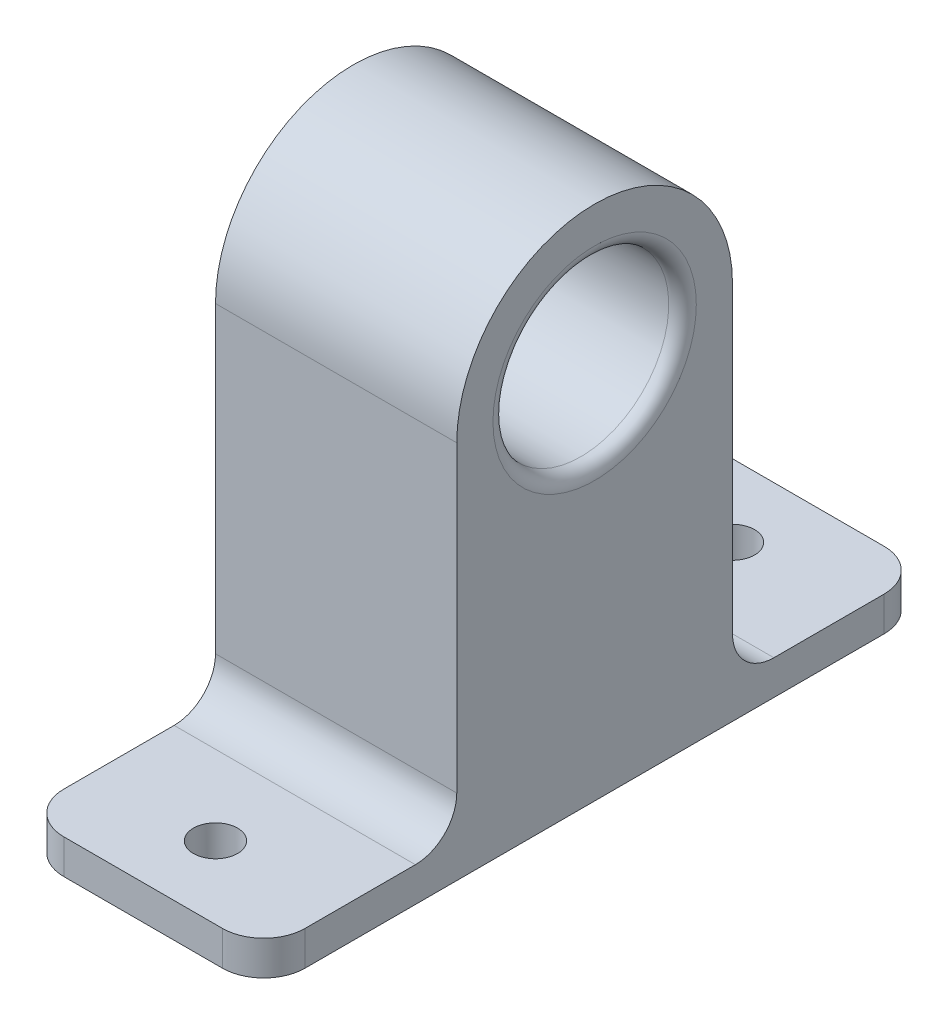
SolidWorks part; units mm, degrees
ref_plane "Front Plane" through (0, 0, 0) normal (0, 0, 1) x (1, 0, 0)
ref_plane "Top Plane" through (0, 0, 0) normal (0, 1, 0) x (1, 0, 0)
ref_plane "Right Plane" through (0, 0, 0) normal (1, 0, 0) x (0, 0, -1)
sketch "Sketch1" plane through (0, 0, 0) normal (1, 0, 0) x (0, 0, -1)
  line L0 (-48, -55) -> (-48, -50)
  line L2 (-37.5, -50) -> (-37.5, -55) construction
  line L3 (-48, -55) -> (48, -55)
  line L6 (-20, 0) -> (-20, -50)
  line L7 (-20, -50) -> (-48, -50)
  line L8 (20, -50) -> (48, -50)
  line L10 (48, -55) -> (48, -50)
  line L12 (37.5, -50) -> (37.5, -55) construction
  line L13 (0, -55) -> (0, 0) construction
  line L14 (20, -50) -> (20, 0)
  circle A0 centre (0, 0) radius 12.75 construction
  arc A1 (-20, 0) -> (20, 0) centre (0, 0) cw
  point P11 (0, -55)
  point P12 (0, 0)
  point P18 (0, 0)
  point P19 (0, 0)
  point P20 (17.7316, -9.2515)
  dimension "D1" = 25.5
  dimension "D2" = 20
  dimension "D5" = 55
  dimension "D6" = 37.5
  dimension "D3" = 28
  dimension "D4" = 5
extrude "Boss-Extrude1" add sketch "Sketch1" along normal blind 35
sketch "Sketch2" plane through (35, 0, 0) normal (1, 0, 0) x (0, 0, -1)
  circle A0 centre (0, 0) radius 12.75 construction
  circle A1 centre (0, 0) radius 12.75
extrude "Cut-Extrude1" cut sketch "Sketch2" against normal offset from surface (32 mm away) 3 up to face at (0, -36.25, 0)
sketch "Sketch3" plane through (0, 0, 0) normal (-1, 0, 0) x (0, 0, 1)
  circle A0 centre (0, 0) radius 8.5 construction
  circle A1 centre (0, 8.5) radius 1.5
  circle A2 centre (0, -8.5) radius 1.5
  circle A3 centre (0, 0) radius 3.75
  dimension "D1" = 17
  dimension "D2" = 7.5
  dimension "D3" = 3
extrude "Cut-Extrude2" cut sketch "Sketch3" against normal up to next
sketch "Sketch4" plane through (0, -50, 0) normal (0, 1, 0) x (1, 0, 0)
  line L0 (17.5, 48) -> (17.5, -48) construction
  line L4 (35, 48) -> (0, 48) construction
  line L5 (35, -48) -> (0, -48) construction
  line L6 (0, 0) -> (35, 0) construction
  line L7 (35, -20) -> (35, 20) construction
  circle A4 centre (17.5, 37.5) radius 3.2
  circle A6 centre (17.5, -37.5) radius 3.2
  dimension "D2" = 6.4
  dimension "D1" = 75
extrude "Cut-Extrude3" cut sketch "Sketch4" against normal up to next
fillet "Fillet1" radius 2 1 edges at (35, 0, -12.75)
fillet "Fillet3" radius 6 2 edges at (17.5, -50, 20) (17.5, -50, -20)
fillet "Fillet4" radius 6 4 edges at (35, -52.5, 48) (0, -52.5, 48) (35, -52.5, -48) (0, -52.5, -48)
